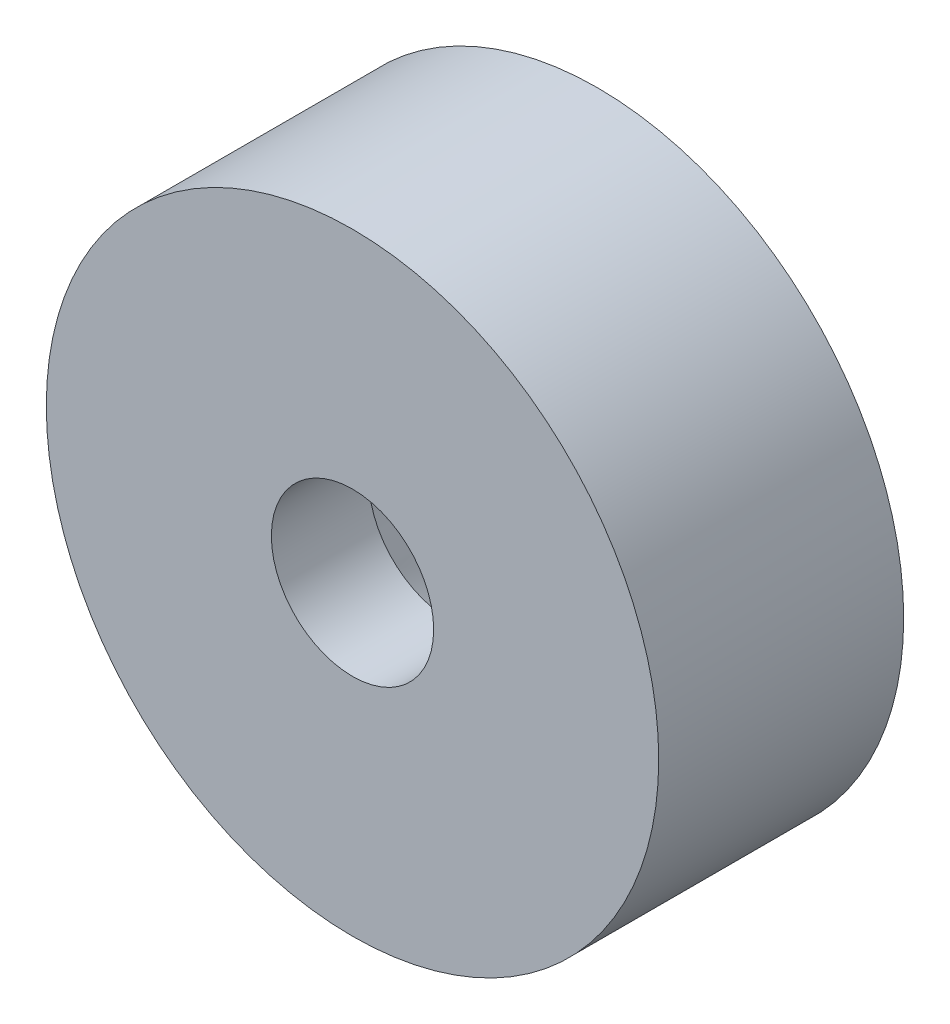
SolidWorks part; units mm, degrees
ref_plane "Front Plane" through (0, 0, 0) normal (0, 0, 1) x (1, 0, 0)
ref_plane "Top Plane" through (0, 0, 0) normal (0, 1, 0) x (1, 0, 0)
ref_plane "Right Plane" through (0, 0, 0) normal (1, 0, 0) x (0, 0, -1)
sketch "Sketch1" plane through (0, 0, 0) normal (0, 0, 1) x (1, 0, 0)
  circle A0 centre (0, 0) radius 10
  dimension "D1" = 20
extrude "Boss-Extrude1" add sketch "Sketch1" along normal blind 8
sketch "Sketch2" plane through (0, 0, 0) normal (0, 0, -1) x (-1, 0, 0)
  circle A0 centre (0, 0) radius 2.65
  dimension "D1" = 5.3
extrude "Cut-Extrude1" cut sketch "Sketch2" against normal up to surface (8 mm away) up to face at (10, 0, 8)
sketch "Sketch3" plane through (0, 0, 0) normal (0, 0, -1) x (-1, 0, 0)
  circle A0 centre (0, 0) radius 5
  dimension "D1" = 10
extrude "Cut-Extrude2" cut sketch "Sketch3" against normal blind 5 draft 26
